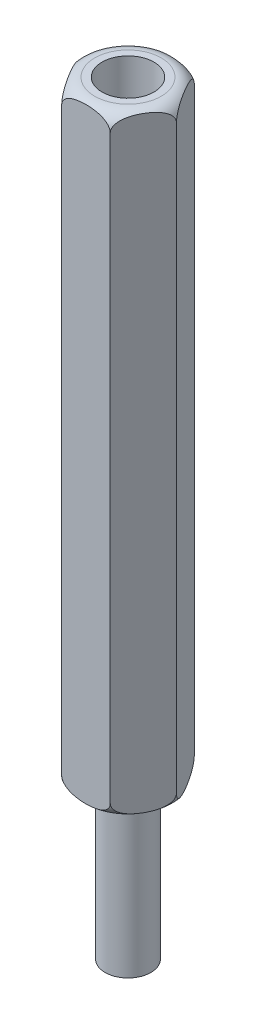
SolidWorks part; units mm, degrees
material "Brass"
ref_plane "Front Plane" through (0, 0, 0) normal (0, 0, 1) x (1, 0, 0)
ref_plane "Top Plane" through (0, 0, 0) normal (0, 1, 0) x (1, 0, 0)
ref_plane "Right Plane" through (0, 0, 0) normal (1, 0, 0) x (0, 0, -1)
sketch "Sketch1" plane through (0, 0, 0) normal (0, 1, 0) x (1, 0, 0)
  line L1 (3.1754, 0) -> (1.5877, 2.75)
  line L2 (1.5877, 2.75) -> (-1.5877, 2.75)
  line L3 (-1.5877, 2.75) -> (-3.1754, 0)
  line L4 (-3.1754, 0) -> (-1.5877, -2.75)
  line L5 (-1.5877, -2.75) -> (1.5877, -2.75)
  line L6 (1.5877, -2.75) -> (3.1754, 0)
  circle A0 centre (0, 0) radius 2.75 construction
  dimension "D1" = 5.5
extrude "Boss-Extrude1" add sketch "Sketch1" along normal blind 40
hole_wizard "M3 Clearance Hole1" positions "Sketch3" profile "Sketch2" hole size "M3" standard "ISO"
sketch "Sketch3" plane through (0, 40, 0) normal (0, 1, 0) x (-1, 0, 0)
  point P0 (0, 0)
sketch "Sketch2" plane through (0, 40, 0) normal (1, 0, 0) x (0, 0, 1)
  line L0 (0, 0) -> (0, 13.0215)
  line L1 (0, 13.0215) -> (1.7, 12)
  line L2 (1.7, 12) -> (1.7, 0)
  line L5 (1.7, 0) -> (0, 0)
  line L10 (0, 13.0215) -> (-1.7, 12) construction
  line L11 (0, -6.35) -> (0, 107.95) construction
  dimension "Hole Dia." = 3.4
  dimension "Hole Depth" = 12
  dimension "Drill Angle" = 118
sketch "Sketch4" plane through (0, 0, 0) normal (0, 0, 1) x (1, 0, 0)
  line L0 (-3.1754, 40) -> (-3.1754, 0) construction
  line L1 (-3.1754, 40) -> (-1.5877, 40) construction
  line L4 (-3.1754, 0) -> (-1.5877, 0) construction
  line L6 (-2.1754, 40) -> (-3.1754, 40)
  line L7 (-3.1754, 40) -> (-3.1754, 39)
  line L8 (-3.1754, 1) -> (-3.1754, 0)
  line L9 (-3.1754, 0) -> (-2.1754, 0)
  line L14 (0, 40) -> (0, 0) construction
  line L15 (-1.5877, 40) -> (1.5877, 40) construction
  arc A0 (-3.1754, 39) -> (-2.1754, 40) centre (-2.1754, 39) cw
  arc A2 (-3.1754, 1) -> (-2.1754, 0) centre (-2.1754, 1) ccw
  dimension "D1" = 1
revolve "Cut-Revolve1" cut sketch "Sketch4" angle 360 about L14
sketch "Sketch5" plane through (0, 0, 0) normal (0, -1, 0) x (1, 0, 0)
  circle A0 centre (0, 0) radius 1.5
  dimension "D1" = 3
extrude "Boss-Extrude2" add sketch "Sketch5" along normal blind 10
